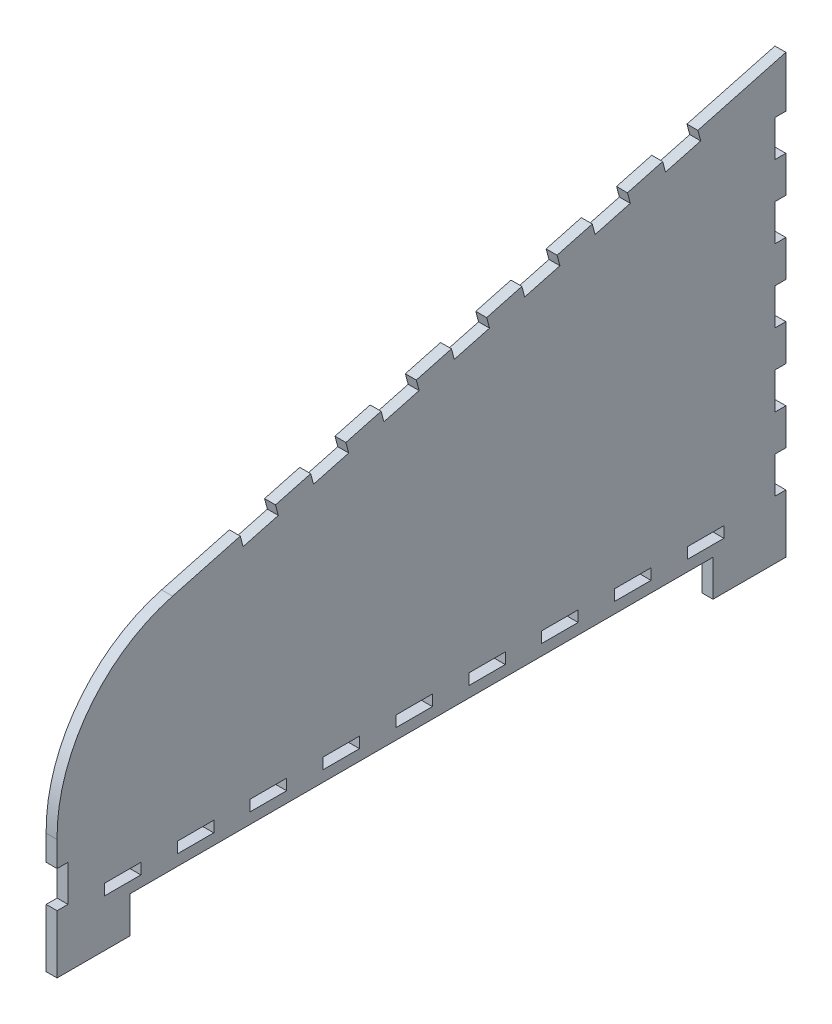
SolidWorks part; units mm, degrees
ref_plane "Front Plane" through (0, 0, 0) normal (0, 0, 1) x (1, 0, 0)
ref_plane "Top Plane" through (0, 0, 0) normal (0, 1, 0) x (1, 0, 0)
ref_plane "Right Plane" through (0, 0, 0) normal (1, 0, 0) x (0, 0, -1)
sketch "Sketch1" plane through (0, 0, 0) normal (1, 0, 0) x (0, 0, -1)
  line L0 (-100, -60) -> (-80, -60)
  line L1 (-80, -60) -> (-80, -50)
  line L2 (-80, -50) -> (80, -50)
  line L3 (80, -50) -> (80, -60)
  line L4 (80, -60) -> (100, -60)
  line L5 (100, -60) -> (100, 60)
  line L6 (100, 60) -> (-68.3022, 14.9036)
  line L7 (-100, -27.0742) -> (-100, -60)
  line L8 (75.8519, 53.5295) -> (76.6283, 50.6317)
  line L9 (100, -34) -> (97, -34)
  line L10 (100, -34) -> (100, -44)
  line L11 (100, -44) -> (97, -44)
  line L12 (97, -34) -> (97, -44)
  line L13 (100, -34) -> (97, -44) construction
  line L14 (100, -44) -> (97, -34) construction
  line L15 (-100, -44) -> (-97, -44)
  line L16 (-100, -44) -> (-100, -34)
  line L17 (-100, -34) -> (-97, -34)
  line L18 (-97, -44) -> (-97, -34)
  line L19 (-100, -44) -> (-97, -34) construction
  line L20 (-100, -34) -> (-97, -44) construction
  line L21 (76.6283, 50.6317) -> (66.9691, 48.0436)
  line L22 (66.9691, 48.0436) -> (66.1926, 50.9413)
  line L23 (100, -24) -> (97, -24)
  line L24 (97, -14) -> (97, -24)
  line L25 (100, -14) -> (97, -14)
  line L26 (100, -4) -> (97, -4)
  line L27 (97, 6) -> (97, -4)
  line L28 (100, 6) -> (97, 6)
  line L29 (100, 16) -> (97, 16)
  line L30 (97, 26) -> (97, 16)
  line L31 (100, 26) -> (97, 26)
  line L32 (100, 36) -> (97, 36)
  line L33 (97, 46) -> (97, 36)
  line L34 (100, 46) -> (97, 46)
  line L35 (100, -44) -> (100, -24) construction
  line L36 (56.5333, 48.3531) -> (57.3098, 45.4554)
  line L37 (57.3098, 45.4554) -> (47.6505, 42.8672)
  line L38 (47.6505, 42.8672) -> (46.8741, 45.765)
  line L39 (37.2148, 43.1768) -> (37.9913, 40.279)
  line L40 (37.9913, 40.279) -> (28.332, 37.6908)
  line L41 (28.332, 37.6908) -> (27.5556, 40.5886)
  line L42 (17.8963, 38.0004) -> (18.6728, 35.1026)
  line L43 (18.6728, 35.1026) -> (9.0135, 32.5144)
  line L44 (9.0135, 32.5144) -> (8.237, 35.4122)
  line L45 (-1.4222, 32.824) -> (-0.6458, 29.9262)
  line L46 (-0.6458, 29.9262) -> (-10.305, 27.338)
  line L47 (-10.305, 27.338) -> (-11.0815, 30.2358)
  line L48 (-20.7407, 27.6476) -> (-19.9643, 24.7498)
  line L49 (-19.9643, 24.7498) -> (-29.6235, 22.1617)
  line L50 (-29.6235, 22.1617) -> (-30.4, 25.0594)
  line L51 (-40.0592, 22.4712) -> (-39.2828, 19.5735)
  line L52 (-39.2828, 19.5735) -> (-48.942, 16.9853)
  line L53 (-48.942, 16.9853) -> (-49.7185, 19.883)
  line L54 (75.8519, 53.5295) -> (56.5333, 48.3531) construction
  line L55 (-97, -47) -> (80, -47) construction
  line L56 (-80, -47) -> (80, -47) construction
  line L57 (-67, -44) -> (-67, -47)
  line L58 (-87, -44) -> (-77, -44)
  line L59 (-87, -44) -> (-87, -47)
  line L60 (-87, -47) -> (-77, -47)
  line L61 (-77, -44) -> (-77, -47)
  line L62 (-87, -44) -> (-77, -47) construction
  line L63 (-87, -47) -> (-77, -44) construction
  line L64 (-67, -44) -> (-57, -44)
  line L65 (-57, -44) -> (-57, -47)
  line L66 (-67, -47) -> (-57, -47)
  line L67 (-47, -44) -> (-47, -47)
  line L68 (-47, -44) -> (-37, -44)
  line L69 (-37, -44) -> (-37, -47)
  line L70 (-47, -47) -> (-37, -47)
  line L71 (-27, -44) -> (-27, -47)
  line L72 (-27, -44) -> (-17, -44)
  line L73 (-17, -44) -> (-17, -47)
  line L74 (-27, -47) -> (-17, -47)
  line L75 (-7, -44) -> (-7, -47)
  line L76 (-7, -44) -> (3, -44)
  line L77 (3, -44) -> (3, -47)
  line L78 (-7, -47) -> (3, -47)
  line L79 (13, -44) -> (13, -47)
  line L80 (13, -44) -> (23, -44)
  line L81 (23, -44) -> (23, -47)
  line L82 (13, -47) -> (23, -47)
  line L83 (33, -44) -> (33, -47)
  line L84 (33, -44) -> (43, -44)
  line L85 (43, -44) -> (43, -47)
  line L86 (33, -47) -> (43, -47)
  line L87 (53, -44) -> (53, -47)
  line L88 (53, -44) -> (63, -44)
  line L89 (63, -44) -> (63, -47)
  line L90 (53, -47) -> (63, -47)
  line L91 (73, -44) -> (73, -47)
  line L92 (73, -44) -> (83, -44)
  line L93 (83, -44) -> (83, -47)
  line L94 (73, -47) -> (83, -47)
  line L95 (-87, -44) -> (-67, -44) construction
  arc A0 (-68.3022, 14.9036) -> (-100, -27.0742) centre (-57.2316, -26.4125) ccw
  point P12 (100, 0)
  point P14 (0, -50)
  point P18 (98.5, -39)
  point P22 (-98.5, -39)
  point P25 (-87, -45.5)
  point P83 (-82, -45.5)
  dimension "D1" = 75
  dimension "D2" = 200
  dimension "D3" = 20
  dimension "D4" = 20
  dimension "D5" = 120
  dimension "D6" = 42.7735
  dimension "D7" = 10
  dimension "D8" = 3
  dimension "D9" = 10
  dimension "D10" = 16
  dimension "D12" = 20
  dimension "D13" = 3
  dimension "D14" = 10
  dimension "D15" = 25
  dimension "D17" = 20
  dimension "D18" = 10
  dimension "D19" = 3
  dimension "D20" = 16
  dimension "D22" = 10
  dimension "D23" = 3
  dimension "D24" = 10
  dimension "D26" = 20
  dimension "D21" = 3
  dimension "D11" = 5
  dimension "D16" = 7
  dimension "D25" = 9
extrude "Boss-Extrude1" add sketch "Sketch1" along normal blind 3 contours L6 A0 L7 L17 L18 L15 L0 L1 L2 L3 L4 L5 L11 L12 L9 L23 L24 L25 L26 L27 L28 L29 L30 L31 L32 L33 L34 L8 L21 L22 L36 L37 L38 L39 L40 L41 L42 L43 L44 L45
